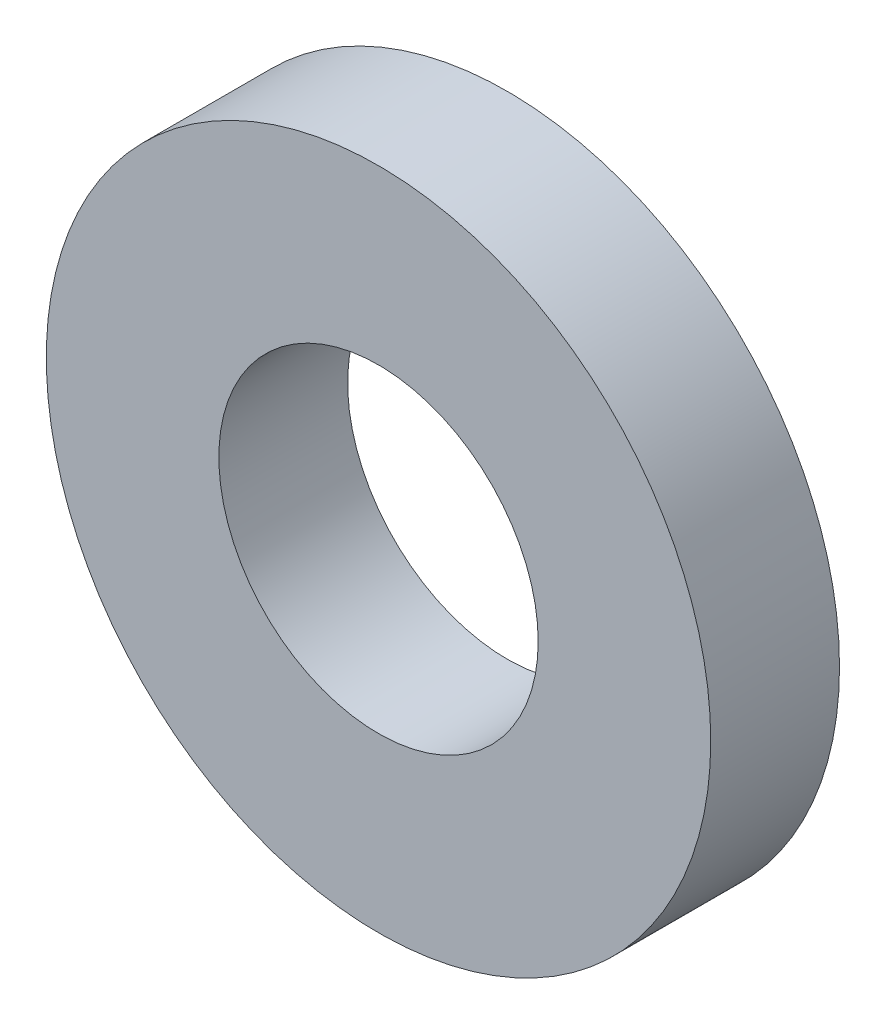
SolidWorks part; units mm, degrees
ref_plane "Plan de face" through (0, 0, 0) normal (0, 0, 1) x (1, 0, 0)
ref_plane "Plan de dessus" through (0, 0, 0) normal (0, 1, 0) x (1, 0, 0)
ref_plane "Plan de droite" through (0, 0, 0) normal (1, 0, 0) x (0, 0, -1)
sketch "Esquisse1" plane through (0, 0, 0) normal (0, 0, 1) x (1, 0, 0)
  circle A0 centre (0, 0) radius 12.9
  circle A1 centre (0, 0) radius 6.2
  dimension "D1" = 25.8
  dimension "D2" = 12.4
extrude "Boss.-Extru.1" add sketch "Esquisse1" along normal blind 5
